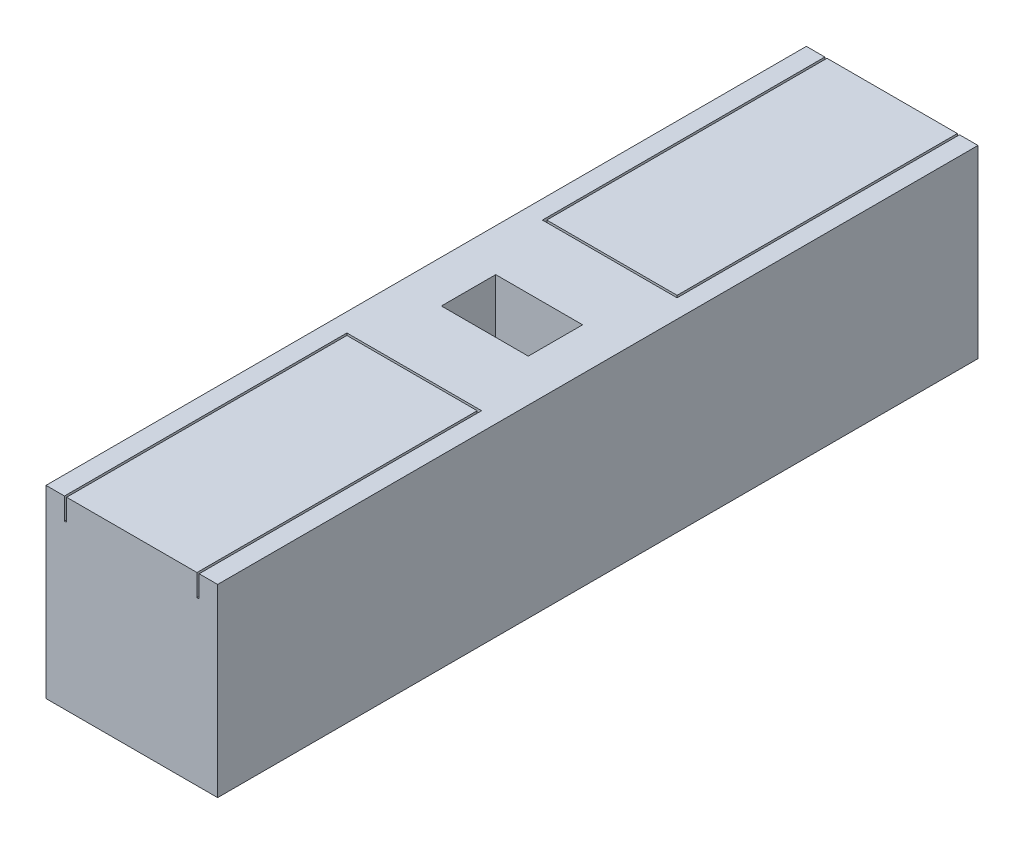
SolidWorks part; units mm, degrees
ref_plane "Front Plane" through (0, 0, 0) normal (0, 0, 1) x (1, 0, 0)
ref_plane "Top Plane" through (0, 0, 0) normal (0, 1, 0) x (1, 0, 0)
ref_plane "Right Plane" through (0, 0, 0) normal (1, 0, 0) x (0, 0, -1)
sketch "Sketch1" plane through (0, 0, 0) normal (0, 0, 1) x (1, 0, 0)
  line L1 (0, 0) -> (7.9, 0)
  line L2 (0, 0) -> (0, 8.5)
  line L3 (0, 8.5) -> (7.9, 8.5)
  line L4 (7.9, 0) -> (7.9, 8.5)
  dimension "D1" = 8.5
  dimension "D2" = 7.9
extrude "Boss-Extrude1" add sketch "Sketch1" along normal blind 35
sketch "Sketch2" plane through (0, 8.5, 0) normal (0, 1, 0) x (1, 0, 0)
  line L0 (7.9, -35) -> (0, -35) construction
  line L1 (0.85, -35) -> (0.95, -35)
  line L2 (0.85, -35) -> (0.85, -22)
  line L3 (0.85, -22) -> (7.05, -22)
  line L4 (7.05, -35) -> (7.05, -22)
  line L5 (0, -17.5) -> (7.9, -17.5) construction
  line L7 (0.95, -35) -> (0.95, -22.1)
  line L8 (0.95, -22.1) -> (6.95, -22.1)
  line L9 (6.95, -35) -> (6.95, -22.1)
  line L10 (0, -35) -> (0, 0) construction
  line L11 (7.9, -35) -> (7.9, 0) construction
  line L12 (6.95, -35) -> (7.05, -35)
  line L13 (6.95, 0) -> (7.05, 0)
  line L14 (6.95, 0) -> (6.95, -12.9)
  line L15 (0.95, -12.9) -> (6.95, -12.9)
  line L16 (0.95, 0) -> (0.95, -12.9)
  line L17 (7.05, 0) -> (7.05, -13)
  line L18 (0.85, -13) -> (7.05, -13)
  line L19 (0.85, 0) -> (0.85, -13)
  line L20 (0.85, 0) -> (0.95, 0)
  point P6 (3.95, -35)
  point P7 (3.95, -22)
  dimension "D1" = 6.2
  dimension "D2" = 13
  dimension "D3" = 0.1
  dimension "D4" = 0.1
  dimension "D5" = 0.1
extrude "Cut-Extrude1" cut sketch "Sketch2" against normal blind 1
sketch "Sketch3" plane through (0, 8.5, 0) normal (0, 1, 0) x (1, 0, 0)
  line L0 (0, -35) -> (0, 0) construction
  line L1 (1.95, -16.25) -> (5.95, -16.25)
  line L2 (1.95, -16.25) -> (1.95, -18.75)
  line L3 (1.95, -18.75) -> (5.95, -18.75)
  line L4 (5.95, -16.25) -> (5.95, -18.75)
  line L5 (6.95, 0) -> (0.95, 0) construction
  point P6 (0, -17.5)
  point P7 (1.95, -17.5)
  point P10 (3.95, 0)
  point P11 (3.95, -16.25)
  dimension "D1" = 4
  dimension "D2" = 2.5
extrude "Cut-Extrude2" cut sketch "Sketch3" against normal blind 3.5
